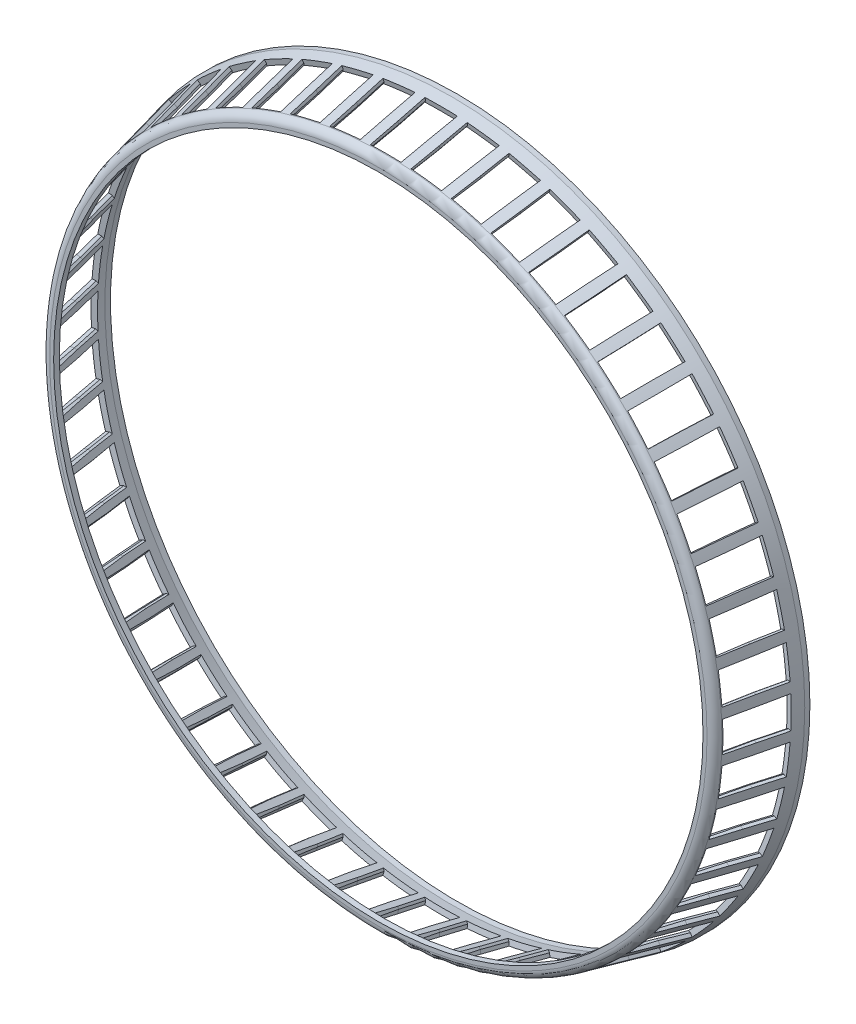
SolidWorks part; units mm, degrees
material "1.0570 (S355J2G3)"
ref_plane "Ebene vorne" through (0, 0, 0) normal (0, 0, 1) x (1, 0, 0)
ref_plane "Ebene oben" through (0, 0, 0) normal (0, 1, 0) x (1, 0, 0)
ref_plane "Ebene rechts" through (0, 0, 0) normal (1, 0, 0) x (0, 0, -1)
sketch "Skizze1" plane through (0, 0, 0) normal (1, 0, 0) x (0, 0, -1)
  line L0 (0, 0) -> (105.2346, 0) construction
  line L1 (0, 0) -> (0, 83.7808) construction
  line L2 (0, 571) -> (0, 578.0685)
  line L3 (11.6257, 592.684) -> (129.9443, 620)
  line L4 (129.9443, 620) -> (139, 620)
  line L5 (139, 620) -> (139, 610)
  line L6 (139, 610) -> (129.1156, 610)
  line L7 (129.1156, 610) -> (13.8752, 583.3947)
  line L8 (10, 578.5228) -> (10, 571)
  line L9 (10, 571) -> (0, 571)
  line L10 (12.8501, 592.9667) -> (15, 583.6543) construction
  line L11 (110.2871, 615.4618) -> (112.437, 606.1494) construction
  line L12 (61.5686, 604.2142) -> (63.7185, 594.9019) construction
  line L13 (12.8501, -592.9667) -> (15, -583.6543) construction
  line L14 (110.2871, -615.4618) -> (112.437, -606.1494) construction
  line L15 (61.5686, -604.2142) -> (63.7185, -594.9019) construction
  line L16 (0, -571) -> (0, -578.0685) construction
  line L17 (10, -571) -> (0, -571) construction
  line L18 (10, -578.5228) -> (10, -571) construction
  line L19 (129.1156, -610) -> (13.8752, -583.3947) construction
  line L20 (139, -610) -> (129.1156, -610) construction
  line L21 (139, -620) -> (139, -610) construction
  line L22 (129.9443, -620) -> (139, -620) construction
  line L23 (11.6257, -592.684) -> (129.9443, -620) construction
  arc A0 (0, 578.0685) -> (11.6257, 592.684) centre (15, 578.0685) cw
  arc A1 (13.8752, 583.3947) -> (10, 578.5228) centre (15, 578.5228) ccw
  arc A2 (0, -578.0685) -> (11.6257, -592.684) centre (15, -578.0685) ccw construction
  arc A3 (13.8752, -583.3947) -> (10, -578.5228) centre (15, -578.5228) cw construction
  point P24 (0, 590)
  point P28 (10, 582.5)
  point P30 (10, -582.5)
  point P31 (0, -590)
  dimension "D8" = 15
  dimension "D9" = 5
  dimension "D10" = 1165
  dimension "D1" = 1240
  dimension "D2" = 139
  dimension "D3" = 13
  dimension "D4" = 1142
  dimension "D5" = 1180
  dimension "D6" = 10
  dimension "D7" = 9.0557
  dimension "D11" = 10
  dimension "D12" = 15
  dimension "D13" = 1185.9333
  dimension "D14" = 1220
  dimension "D15" = 100
  dimension "D16" = 50
  dimension "D17" = 9.5573
  dimension "D18" = 13
revolve "Rotation1" add sketch "Skizze1" angle 360 about L0
ref_plane "Ebene1" through (0, 604.2142, -61.5686) normal (0, -0.9744, -0.225) x (-1, 0, 0)
sketch "Skizze2" plane through (0, 604.2142, -61.5686) normal (0, -0.9744, -0.225) x (-1, 0, 0)
  line L0 (28.5, 50) -> (-28.5, 50)
  line L2 (0, 0) -> (0, 19.02) construction
  line L3 (27.5, 0) -> (-27.5, 0) construction
  line L4 (28.5, 50) -> (27.5, 0)
  line L5 (27.5, 0) -> (27, -50)
  line L6 (27, -50) -> (-27, -50)
  line L7 (-27.5, 0) -> (-27, -50)
  line L8 (-28.5, 50) -> (-27.5, 0)
  point P0 (22.302, 47.521)
  dimension "D4" = 54
  dimension "D2" = 57
  dimension "D3" = 50
  dimension "D6" = 55
  dimension "D11" = 100
extrude "Schnitt-Linear austragen1" cut sketch "Skizze2" along normal blind 30
ref_plane "Ebene2" through (-254.4022, 410.4369, 94.7568) normal (0.517, -0.8341, -0.1926) x (0, 0.225, -0.9744)
sketch "Skizze3" plane through (-254.4022, 410.4369, 94.7568) normal (0.517, -0.8341, -0.1926) x (0, 0.225, -0.9744)
  line L0 (245.9092, 306.1991) -> (145.9092, 306.1991)
  line L1 (195.9092, 297.1991) -> (195.9092, 521.0223) construction
  line L2 (245.9092, 297.1991) -> (145.9092, 297.1991) construction
  line L3 (245.9092, 316.3165) -> (245.9092, 267.5246) construction
  line L4 (195.9092, 317.1991) -> (245.9092, 318.1991)
  line L5 (195.9092, 317.1991) -> (145.9092, 317.6991)
  line L6 (195.9092, 315.4779) -> (195.9092, 320.4237) construction
  line L7 (145.9092, 273.7774) -> (145.9092, 320.0013) construction
  line L8 (245.9092, 321.2626) -> (245.9092, 272.4706) construction
  line L9 (145.9092, 317.6991) -> (145.9092, 306.1991)
  line L10 (245.9092, 318.1991) -> (245.9092, 306.1991)
  line L11 (145.9092, 268.8315) -> (145.9092, 315.0555) construction
  dimension "D4" = 21
  dimension "D2" = 20.5
  dimension "D3" = 18
  dimension "D8" = 50
  dimension "D12" = 20
extrude "Schnitt-Linear austragen2" cut sketch "Skizze3" along normal blind 30
mirror "Spiegeln2" about plane through (0, 0, 0) normal (1, 0, 0) of "Schnitt-Linear austragen2"
pattern_circular "Kreismuster1" count 52 over 360 about axis through (0, 0, 0) along (0, 0, 1) of "Schnitt-Linear austragen1", "Schnitt-Linear austragen2", "Spiegeln2"
sketch3d "3D-Skizze1"
  line L0 (0, 0, -33) -> (0, 89.39, -33) construction
  line L1 (0, 0, 0) -> (0, 0, -105.2346) construction
  line L2 (0, 0, -69) -> (0, 94.2534, -69) construction
  line L3 (0, 0, -101) -> (0, 81.6564, -101) construction
  circle A0 centre (0, 571.8906, -33) radius 33.5 construction
  circle A1 centre (0, 579.8016, -69) radius 33.5 construction
  circle A2 centre (0, 588.5051, -101) radius 33.5 construction
  circle A4 centre (0, 0, -69) radius 613.3016 construction
  circle A5 centre (0, 0, -33) radius 605.3906 construction
  circle A6 centre (0, 0, -101) radius 622.0051 construction
  point P11 (0, 571.8906, 0.5)
  point P14 (0, 579.8016, -35.5)
  point P17 (0, 588.5051, -67.5)
  point P20 (0, 0, 544.3016)
  point P23 (0, 0, 521.0051)
  point P26 (0, 0, 572.3906)
  dimension "D4" = 67
  dimension "D5" = 1210.7813
  dimension "D6" = 1226.6033
  dimension "D7" = 1244.0102
  dimension "D1" = 33
  dimension "D2" = 69
  dimension "D3" = 101
